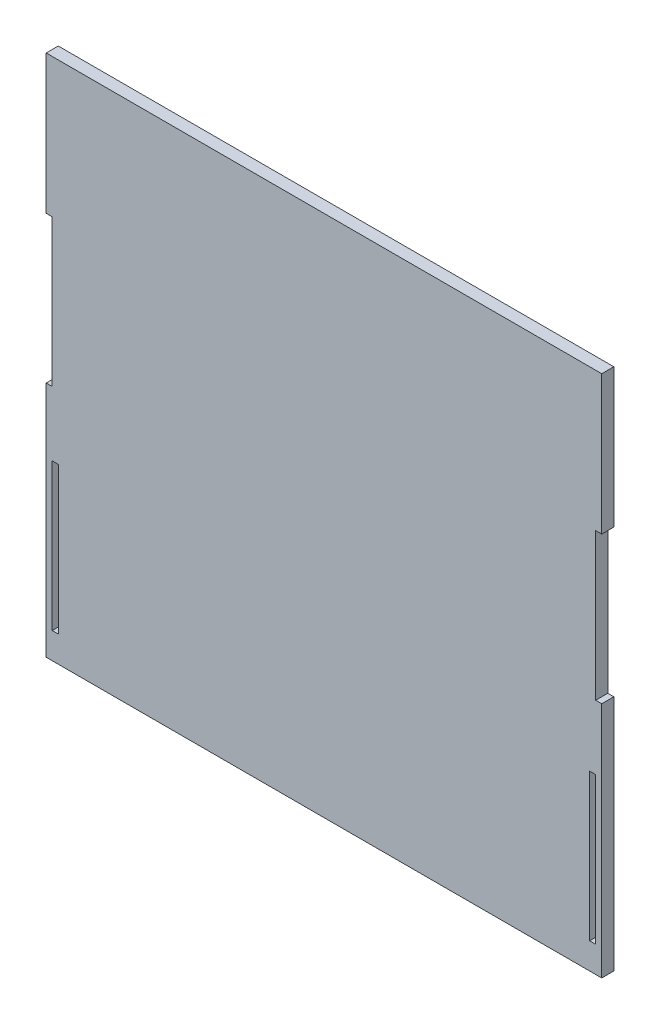
SolidWorks part; units mm, degrees
ref_plane "Front Plane" through (0, 0, 0) normal (0, 0, 1) x (1, 0, 0)
ref_plane "Top Plane" through (0, 0, 0) normal (0, 1, 0) x (1, 0, 0)
ref_plane "Right Plane" through (0, 0, 0) normal (1, 0, 0) x (0, 0, -1)
sketch "Sketch1" plane through (0, 0, 0) normal (0, 0, 1) x (1, 0, 0)
  line L1 (0, 0) -> (138, 0)
  line L2 (0, 0) -> (0, 130)
  line L3 (0, 130) -> (138, 130)
  line L4 (138, 0) -> (138, 130)
  line L5 (138, 95.5) -> (136.5, 95.5)
  line L6 (138, 95.5) -> (138, 59)
  line L7 (138, 59) -> (136.5, 59)
  line L8 (136.5, 95.5) -> (136.5, 59)
  line L9 (136.5, 43) -> (135, 43)
  line L10 (136.5, 43) -> (136.5, 6.5)
  line L11 (136.5, 6.5) -> (135, 6.5)
  line L12 (135, 43) -> (135, 6.5)
  line L13 (3, 43) -> (1.5, 43)
  line L14 (3, 43) -> (3, 6.5)
  line L15 (3, 6.5) -> (1.5, 6.5)
  line L16 (1.5, 43) -> (1.5, 6.5)
  line L17 (0, 95.5) -> (1.5, 95.5)
  line L18 (0, 95.5) -> (0, 59)
  line L19 (0, 59) -> (1.5, 59)
  line L20 (1.5, 95.5) -> (1.5, 59)
  point P21 (135.0557, 46.5863)
  dimension "D1" = 138
  dimension "D2" = 130
  dimension "D3" = 36.5
  dimension "D4" = 135
  dimension "D5" = 1.5
  dimension "D6" = 6.5
  dimension "D7" = 6.5
  dimension "D8" = 1.5
  dimension "D9" = 16
  dimension "D10" = 16
extrude "Boss-Extrude1" add sketch "Sketch1" along normal blind 3 contours L17 L20 L19 L2 L1 L4 L7 L8 L5 L3 L16 L13 L14 L15 L12 L9 L10 L11
